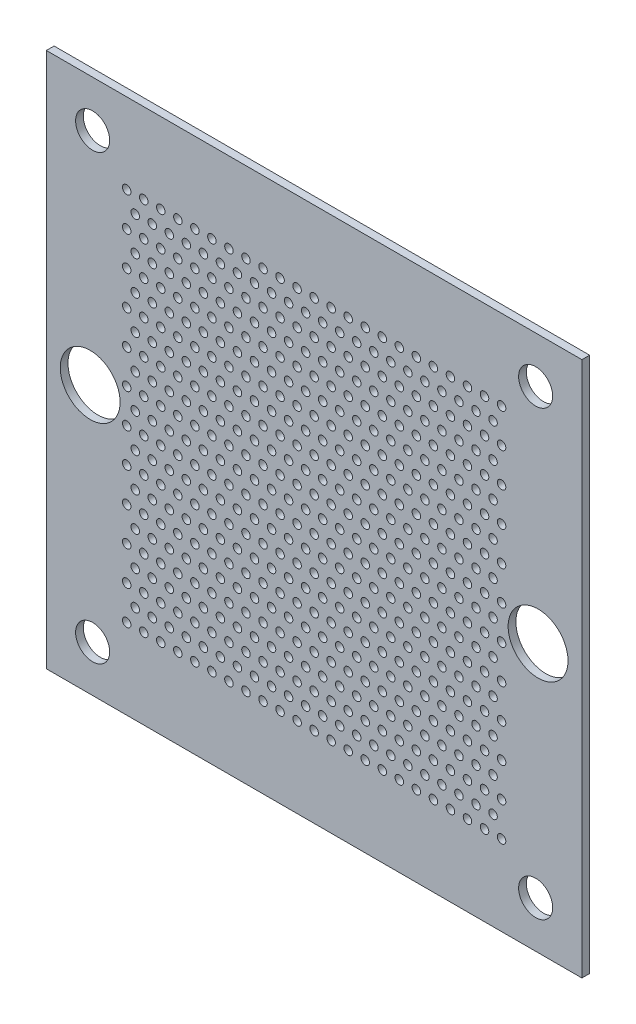
SolidWorks part; units mm, degrees
ref_plane "Front Plane" through (0, 0, 0) normal (0, 0, 1) x (1, 0, 0)
ref_plane "Top Plane" through (0, 0, 0) normal (0, 1, 0) x (1, 0, 0)
ref_plane "Right Plane" through (0, 0, 0) normal (1, 0, 0) x (0, 0, -1)
sketch "Model" plane through (0, 0, 0) normal (0, 0, 1) x (1, 0, 0)
  line L0 (-16.5, -16.5) -> (-16.5, 93.5)
  line L1 (-16.5, 93.5) -> (93.5, 93.5)
  line L2 (93.5, 93.5) -> (93.5, -16.5)
  line L3 (93.5, -16.5) -> (-16.5, -16.5)
  circle A0 centre (84, 84) radius 3.5
  circle A1 centre (-7, 84) radius 3.5
  circle A2 centre (-7, -7) radius 3.5
  circle A3 centre (84, -7) radius 3.5
  circle A4 centre (77, 0) radius 0.875
  circle A5 centre (73.5, 0) radius 0.875
  circle A6 centre (70, 0) radius 0.875
  circle A7 centre (66.5, 0) radius 0.875
  circle A8 centre (63, 0) radius 0.875
  circle A9 centre (59.5, 0) radius 0.875
  circle A10 centre (56, 0) radius 0.875
  circle A11 centre (52.5, 0) radius 0.875
  circle A12 centre (49, 0) radius 0.875
  circle A13 centre (45.5, 0) radius 0.875
  circle A14 centre (42, 0) radius 0.875
  circle A15 centre (38.5, 0) radius 0.875
  circle A16 centre (35, 0) radius 0.875
  circle A17 centre (31.5, 0) radius 0.875
  circle A18 centre (28, 0) radius 0.875
  circle A19 centre (24.5, 0) radius 0.875
  circle A20 centre (21, 0) radius 0.875
  circle A21 centre (17.5, 0) radius 0.875
  circle A22 centre (14, 0) radius 0.875
  circle A23 centre (10.5, 0) radius 0.875
  circle A24 centre (7, 0) radius 0.875
  circle A25 centre (3.5, 0) radius 0.875
  circle A26 centre (0, 0) radius 0.875
  circle A27 centre (75.25, 3.5) radius 0.875
  circle A28 centre (71.75, 3.5) radius 0.875
  circle A29 centre (68.25, 3.5) radius 0.875
  circle A30 centre (64.75, 3.5) radius 0.875
  circle A31 centre (61.25, 3.5) radius 0.875
  circle A32 centre (57.75, 3.5) radius 0.875
  circle A33 centre (54.25, 3.5) radius 0.875
  circle A34 centre (50.75, 3.5) radius 0.875
  circle A35 centre (47.25, 3.5) radius 0.875
  circle A36 centre (43.75, 3.5) radius 0.875
  circle A37 centre (40.25, 3.5) radius 0.875
  circle A38 centre (36.75, 3.5) radius 0.875
  circle A39 centre (33.25, 3.5) radius 0.875
  circle A40 centre (29.75, 3.5) radius 0.875
  circle A41 centre (26.25, 3.5) radius 0.875
  circle A42 centre (22.75, 3.5) radius 0.875
  circle A43 centre (19.25, 3.5) radius 0.875
  circle A44 centre (15.75, 3.5) radius 0.875
  circle A45 centre (12.25, 3.5) radius 0.875
  circle A46 centre (8.75, 3.5) radius 0.875
  circle A47 centre (5.25, 3.5) radius 0.875
  circle A48 centre (1.75, 3.5) radius 0.875
  circle A49 centre (77, 7) radius 0.875
  circle A50 centre (73.5, 7) radius 0.875
  circle A51 centre (70, 7) radius 0.875
  circle A52 centre (66.5, 7) radius 0.875
  circle A53 centre (63, 7) radius 0.875
  circle A54 centre (59.5, 7) radius 0.875
  circle A55 centre (56, 7) radius 0.875
  circle A56 centre (52.5, 7) radius 0.875
  circle A57 centre (49, 7) radius 0.875
  circle A58 centre (45.5, 7) radius 0.875
  circle A59 centre (42, 7) radius 0.875
  circle A60 centre (38.5, 7) radius 0.875
  circle A61 centre (35, 7) radius 0.875
  circle A62 centre (31.5, 7) radius 0.875
  circle A63 centre (28, 7) radius 0.875
  circle A64 centre (24.5, 7) radius 0.875
  circle A65 centre (21, 7) radius 0.875
  circle A66 centre (17.5, 7) radius 0.875
  circle A67 centre (14, 7) radius 0.875
  circle A68 centre (10.5, 7) radius 0.875
  circle A69 centre (7, 7) radius 0.875
  circle A70 centre (3.5, 7) radius 0.875
  circle A71 centre (0, 7) radius 0.875
  circle A72 centre (75.25, 10.5) radius 0.875
  circle A73 centre (71.75, 10.5) radius 0.875
  circle A74 centre (68.25, 10.5) radius 0.875
  circle A75 centre (64.75, 10.5) radius 0.875
  circle A76 centre (61.25, 10.5) radius 0.875
  circle A77 centre (57.75, 10.5) radius 0.875
  circle A78 centre (54.25, 10.5) radius 0.875
  circle A79 centre (50.75, 10.5) radius 0.875
  circle A80 centre (47.25, 10.5) radius 0.875
  circle A81 centre (43.75, 10.5) radius 0.875
  circle A82 centre (40.25, 10.5) radius 0.875
  circle A83 centre (36.75, 10.5) radius 0.875
  circle A84 centre (33.25, 10.5) radius 0.875
  circle A85 centre (29.75, 10.5) radius 0.875
  circle A86 centre (26.25, 10.5) radius 0.875
  circle A87 centre (22.75, 10.5) radius 0.875
  circle A88 centre (19.25, 10.5) radius 0.875
  circle A89 centre (15.75, 10.5) radius 0.875
  circle A90 centre (12.25, 10.5) radius 0.875
  circle A91 centre (8.75, 10.5) radius 0.875
  circle A92 centre (5.25, 10.5) radius 0.875
  circle A93 centre (1.75, 10.5) radius 0.875
  circle A94 centre (77, 14) radius 0.875
  circle A95 centre (73.5, 14) radius 0.875
  circle A96 centre (70, 14) radius 0.875
  circle A97 centre (66.5, 14) radius 0.875
  circle A98 centre (63, 14) radius 0.875
  circle A99 centre (59.5, 14) radius 0.875
  circle A100 centre (56, 14) radius 0.875
  circle A101 centre (52.5, 14) radius 0.875
  circle A102 centre (49, 14) radius 0.875
  circle A103 centre (45.5, 14) radius 0.875
  circle A104 centre (42, 14) radius 0.875
  circle A105 centre (38.5, 14) radius 0.875
  circle A106 centre (35, 14) radius 0.875
  circle A107 centre (31.5, 14) radius 0.875
  circle A108 centre (28, 14) radius 0.875
  circle A109 centre (24.5, 14) radius 0.875
  circle A110 centre (21, 14) radius 0.875
  circle A111 centre (17.5, 14) radius 0.875
  circle A112 centre (14, 14) radius 0.875
  circle A113 centre (10.5, 14) radius 0.875
  circle A114 centre (7, 14) radius 0.875
  circle A115 centre (3.5, 14) radius 0.875
  circle A116 centre (0, 14) radius 0.875
  circle A117 centre (75.25, 17.5) radius 0.875
  circle A118 centre (71.75, 17.5) radius 0.875
  circle A119 centre (68.25, 17.5) radius 0.875
  circle A120 centre (64.75, 17.5) radius 0.875
  circle A121 centre (61.25, 17.5) radius 0.875
  circle A122 centre (57.75, 17.5) radius 0.875
  circle A123 centre (54.25, 17.5) radius 0.875
  circle A124 centre (50.75, 17.5) radius 0.875
  circle A125 centre (47.25, 17.5) radius 0.875
  circle A126 centre (43.75, 17.5) radius 0.875
  circle A127 centre (40.25, 17.5) radius 0.875
  circle A128 centre (36.75, 17.5) radius 0.875
  circle A129 centre (33.25, 17.5) radius 0.875
  circle A130 centre (29.75, 17.5) radius 0.875
  circle A131 centre (26.25, 17.5) radius 0.875
  circle A132 centre (22.75, 17.5) radius 0.875
  circle A133 centre (19.25, 17.5) radius 0.875
  circle A134 centre (15.75, 17.5) radius 0.875
  circle A135 centre (12.25, 17.5) radius 0.875
  circle A136 centre (8.75, 17.5) radius 0.875
  circle A137 centre (5.25, 17.5) radius 0.875
  circle A138 centre (1.75, 17.5) radius 0.875
  circle A139 centre (77, 21) radius 0.875
  circle A140 centre (73.5, 21) radius 0.875
  circle A141 centre (70, 21) radius 0.875
  circle A142 centre (66.5, 21) radius 0.875
  circle A143 centre (63, 21) radius 0.875
  circle A144 centre (59.5, 21) radius 0.875
  circle A145 centre (56, 21) radius 0.875
  circle A146 centre (52.5, 21) radius 0.875
  circle A147 centre (49, 21) radius 0.875
  circle A148 centre (45.5, 21) radius 0.875
  circle A149 centre (42, 21) radius 0.875
  circle A150 centre (38.5, 21) radius 0.875
  circle A151 centre (35, 21) radius 0.875
  circle A152 centre (31.5, 21) radius 0.875
  circle A153 centre (28, 21) radius 0.875
  circle A154 centre (24.5, 21) radius 0.875
  circle A155 centre (21, 21) radius 0.875
  circle A156 centre (17.5, 21) radius 0.875
  circle A157 centre (14, 21) radius 0.875
  circle A158 centre (10.5, 21) radius 0.875
  circle A159 centre (7, 21) radius 0.875
  circle A160 centre (3.5, 21) radius 0.875
  circle A161 centre (0, 21) radius 0.875
  circle A162 centre (75.25, 24.5) radius 0.875
  circle A163 centre (71.75, 24.5) radius 0.875
  circle A164 centre (68.25, 24.5) radius 0.875
  circle A165 centre (64.75, 24.5) radius 0.875
  circle A166 centre (61.25, 24.5) radius 0.875
  circle A167 centre (57.75, 24.5) radius 0.875
  circle A168 centre (54.25, 24.5) radius 0.875
  circle A169 centre (50.75, 24.5) radius 0.875
  circle A170 centre (47.25, 24.5) radius 0.875
  circle A171 centre (43.75, 24.5) radius 0.875
  circle A172 centre (40.25, 24.5) radius 0.875
  circle A173 centre (36.75, 24.5) radius 0.875
  circle A174 centre (33.25, 24.5) radius 0.875
  circle A175 centre (29.75, 24.5) radius 0.875
  circle A176 centre (26.25, 24.5) radius 0.875
  circle A177 centre (22.75, 24.5) radius 0.875
  circle A178 centre (19.25, 24.5) radius 0.875
  circle A179 centre (15.75, 24.5) radius 0.875
  circle A180 centre (12.25, 24.5) radius 0.875
  circle A181 centre (8.75, 24.5) radius 0.875
  circle A182 centre (5.25, 24.5) radius 0.875
  circle A183 centre (1.75, 24.5) radius 0.875
  circle A184 centre (77, 28) radius 0.875
  circle A185 centre (73.5, 28) radius 0.875
  circle A186 centre (70, 28) radius 0.875
  circle A187 centre (66.5, 28) radius 0.875
  circle A188 centre (63, 28) radius 0.875
  circle A189 centre (59.5, 28) radius 0.875
  circle A190 centre (56, 28) radius 0.875
  circle A191 centre (52.5, 28) radius 0.875
  circle A192 centre (49, 28) radius 0.875
  circle A193 centre (45.5, 28) radius 0.875
  circle A194 centre (42, 28) radius 0.875
  circle A195 centre (38.5, 28) radius 0.875
  circle A196 centre (35, 28) radius 0.875
  circle A197 centre (31.5, 28) radius 0.875
  circle A198 centre (28, 28) radius 0.875
  circle A199 centre (24.5, 28) radius 0.875
  circle A200 centre (21, 28) radius 0.875
  circle A201 centre (17.5, 28) radius 0.875
  circle A202 centre (14, 28) radius 0.875
  circle A203 centre (10.5, 28) radius 0.875
  circle A204 centre (7, 28) radius 0.875
  circle A205 centre (3.5, 28) radius 0.875
  circle A206 centre (0, 28) radius 0.875
  circle A207 centre (75.25, 31.5) radius 0.875
  circle A208 centre (71.75, 31.5) radius 0.875
  circle A209 centre (68.25, 31.5) radius 0.875
  circle A210 centre (64.75, 31.5) radius 0.875
  circle A211 centre (61.25, 31.5) radius 0.875
  circle A212 centre (57.75, 31.5) radius 0.875
  circle A213 centre (54.25, 31.5) radius 0.875
  circle A214 centre (50.75, 31.5) radius 0.875
  circle A215 centre (47.25, 31.5) radius 0.875
  circle A216 centre (43.75, 31.5) radius 0.875
  circle A217 centre (40.25, 31.5) radius 0.875
  circle A218 centre (36.75, 31.5) radius 0.875
  circle A219 centre (33.25, 31.5) radius 0.875
  circle A220 centre (29.75, 31.5) radius 0.875
  circle A221 centre (26.25, 31.5) radius 0.875
  circle A222 centre (22.75, 31.5) radius 0.875
  circle A223 centre (19.25, 31.5) radius 0.875
  circle A224 centre (15.75, 31.5) radius 0.875
  circle A225 centre (12.25, 31.5) radius 0.875
  circle A226 centre (8.75, 31.5) radius 0.875
  circle A227 centre (5.25, 31.5) radius 0.875
  circle A228 centre (1.75, 31.5) radius 0.875
  circle A229 centre (77, 35) radius 0.875
  circle A230 centre (73.5, 35) radius 0.875
  circle A231 centre (70, 35) radius 0.875
  circle A232 centre (66.5, 35) radius 0.875
  circle A233 centre (63, 35) radius 0.875
  circle A234 centre (59.5, 35) radius 0.875
  circle A235 centre (56, 35) radius 0.875
  circle A236 centre (52.5, 35) radius 0.875
  circle A237 centre (49, 35) radius 0.875
  circle A238 centre (45.5, 35) radius 0.875
  circle A239 centre (42, 35) radius 0.875
  circle A240 centre (38.5, 35) radius 0.875
  circle A241 centre (35, 35) radius 0.875
  circle A242 centre (31.5, 35) radius 0.875
  circle A243 centre (28, 35) radius 0.875
  circle A244 centre (24.5, 35) radius 0.875
  circle A245 centre (21, 35) radius 0.875
  circle A246 centre (17.5, 35) radius 0.875
  circle A247 centre (14, 35) radius 0.875
  circle A248 centre (10.5, 35) radius 0.875
  circle A249 centre (7, 35) radius 0.875
  circle A250 centre (3.5, 35) radius 0.875
  circle A251 centre (0, 35) radius 0.875
  circle A252 centre (75.25, 38.5) radius 0.875
  circle A253 centre (71.75, 38.5) radius 0.875
  circle A254 centre (68.25, 38.5) radius 0.875
  circle A255 centre (64.75, 38.5) radius 0.875
  circle A256 centre (61.25, 38.5) radius 0.875
  circle A257 centre (57.75, 38.5) radius 0.875
  circle A258 centre (54.25, 38.5) radius 0.875
  circle A259 centre (50.75, 38.5) radius 0.875
  circle A260 centre (47.25, 38.5) radius 0.875
  circle A261 centre (43.75, 38.5) radius 0.875
  circle A262 centre (40.25, 38.5) radius 0.875
  circle A263 centre (36.75, 38.5) radius 0.875
  circle A264 centre (33.25, 38.5) radius 0.875
  circle A265 centre (29.75, 38.5) radius 0.875
  circle A266 centre (26.25, 38.5) radius 0.875
  circle A267 centre (22.75, 38.5) radius 0.875
  circle A268 centre (19.25, 38.5) radius 0.875
  circle A269 centre (15.75, 38.5) radius 0.875
  circle A270 centre (12.25, 38.5) radius 0.875
  circle A271 centre (8.75, 38.5) radius 0.875
  circle A272 centre (5.25, 38.5) radius 0.875
  circle A273 centre (1.75, 38.5) radius 0.875
  circle A274 centre (77, 42) radius 0.875
  circle A275 centre (73.5, 42) radius 0.875
  circle A276 centre (70, 42) radius 0.875
  circle A277 centre (66.5, 42) radius 0.875
  circle A278 centre (63, 42) radius 0.875
  circle A279 centre (59.5, 42) radius 0.875
  circle A280 centre (56, 42) radius 0.875
  circle A281 centre (52.5, 42) radius 0.875
  circle A282 centre (49, 42) radius 0.875
  circle A283 centre (45.5, 42) radius 0.875
  circle A284 centre (42, 42) radius 0.875
  circle A285 centre (38.5, 42) radius 0.875
  circle A286 centre (35, 42) radius 0.875
  circle A287 centre (31.5, 42) radius 0.875
  circle A288 centre (28, 42) radius 0.875
  circle A289 centre (24.5, 42) radius 0.875
  circle A290 centre (21, 42) radius 0.875
  circle A291 centre (17.5, 42) radius 0.875
  circle A292 centre (14, 42) radius 0.875
  circle A293 centre (10.5, 42) radius 0.875
  circle A294 centre (7, 42) radius 0.875
  circle A295 centre (3.5, 42) radius 0.875
  circle A296 centre (0, 42) radius 0.875
  circle A297 centre (75.25, 45.5) radius 0.875
  circle A298 centre (71.75, 45.5) radius 0.875
  circle A299 centre (68.25, 45.5) radius 0.875
  circle A300 centre (64.75, 45.5) radius 0.875
  circle A301 centre (61.25, 45.5) radius 0.875
  circle A302 centre (57.75, 45.5) radius 0.875
  circle A303 centre (54.25, 45.5) radius 0.875
  circle A304 centre (50.75, 45.5) radius 0.875
  circle A305 centre (47.25, 45.5) radius 0.875
  circle A306 centre (43.75, 45.5) radius 0.875
  circle A307 centre (40.25, 45.5) radius 0.875
  circle A308 centre (36.75, 45.5) radius 0.875
  circle A309 centre (33.25, 45.5) radius 0.875
  circle A310 centre (29.75, 45.5) radius 0.875
  circle A311 centre (26.25, 45.5) radius 0.875
  circle A312 centre (22.75, 45.5) radius 0.875
  circle A313 centre (19.25, 45.5) radius 0.875
  circle A314 centre (15.75, 45.5) radius 0.875
  circle A315 centre (12.25, 45.5) radius 0.875
  circle A316 centre (8.75, 45.5) radius 0.875
  circle A317 centre (5.25, 45.5) radius 0.875
  circle A318 centre (1.75, 45.5) radius 0.875
  circle A319 centre (77, 49) radius 0.875
  circle A320 centre (73.5, 49) radius 0.875
  circle A321 centre (70, 49) radius 0.875
  circle A322 centre (66.5, 49) radius 0.875
  circle A323 centre (63, 49) radius 0.875
  circle A324 centre (59.5, 49) radius 0.875
  circle A325 centre (56, 49) radius 0.875
  circle A326 centre (52.5, 49) radius 0.875
  circle A327 centre (49, 49) radius 0.875
  circle A328 centre (45.5, 49) radius 0.875
  circle A329 centre (42, 49) radius 0.875
  circle A330 centre (38.5, 49) radius 0.875
  circle A331 centre (35, 49) radius 0.875
  circle A332 centre (31.5, 49) radius 0.875
  circle A333 centre (28, 49) radius 0.875
  circle A334 centre (24.5, 49) radius 0.875
  circle A335 centre (21, 49) radius 0.875
  circle A336 centre (17.5, 49) radius 0.875
  circle A337 centre (14, 49) radius 0.875
  circle A338 centre (10.5, 49) radius 0.875
  circle A339 centre (7, 49) radius 0.875
  circle A340 centre (3.5, 49) radius 0.875
  circle A341 centre (0, 49) radius 0.875
  circle A342 centre (75.25, 52.5) radius 0.875
  circle A343 centre (71.75, 52.5) radius 0.875
  circle A344 centre (68.25, 52.5) radius 0.875
  circle A345 centre (64.75, 52.5) radius 0.875
  circle A346 centre (61.25, 52.5) radius 0.875
  circle A347 centre (57.75, 52.5) radius 0.875
  circle A348 centre (54.25, 52.5) radius 0.875
  circle A349 centre (50.75, 52.5) radius 0.875
  circle A350 centre (47.25, 52.5) radius 0.875
  circle A351 centre (43.75, 52.5) radius 0.875
  circle A352 centre (40.25, 52.5) radius 0.875
  circle A353 centre (36.75, 52.5) radius 0.875
  circle A354 centre (33.25, 52.5) radius 0.875
  circle A355 centre (29.75, 52.5) radius 0.875
  circle A356 centre (26.25, 52.5) radius 0.875
  circle A357 centre (22.75, 52.5) radius 0.875
  circle A358 centre (19.25, 52.5) radius 0.875
  circle A359 centre (15.75, 52.5) radius 0.875
  circle A360 centre (12.25, 52.5) radius 0.875
  circle A361 centre (8.75, 52.5) radius 0.875
  circle A362 centre (5.25, 52.5) radius 0.875
  circle A363 centre (1.75, 52.5) radius 0.875
  circle A364 centre (77, 56) radius 0.875
  circle A365 centre (73.5, 56) radius 0.875
  circle A366 centre (70, 56) radius 0.875
  circle A367 centre (66.5, 56) radius 0.875
  circle A368 centre (63, 56) radius 0.875
  circle A369 centre (59.5, 56) radius 0.875
  circle A370 centre (56, 56) radius 0.875
  circle A371 centre (52.5, 56) radius 0.875
  circle A372 centre (49, 56) radius 0.875
  circle A373 centre (45.5, 56) radius 0.875
  circle A374 centre (42, 56) radius 0.875
  circle A375 centre (38.5, 56) radius 0.875
  circle A376 centre (35, 56) radius 0.875
  circle A377 centre (31.5, 56) radius 0.875
  circle A378 centre (28, 56) radius 0.875
  circle A379 centre (24.5, 56) radius 0.875
  circle A380 centre (21, 56) radius 0.875
  circle A381 centre (17.5, 56) radius 0.875
  circle A382 centre (14, 56) radius 0.875
  circle A383 centre (10.5, 56) radius 0.875
  circle A384 centre (7, 56) radius 0.875
  circle A385 centre (3.5, 56) radius 0.875
  circle A386 centre (0, 56) radius 0.875
  circle A387 centre (75.25, 59.5) radius 0.875
  circle A388 centre (71.75, 59.5) radius 0.875
  circle A389 centre (68.25, 59.5) radius 0.875
  circle A390 centre (64.75, 59.5) radius 0.875
  circle A391 centre (61.25, 59.5) radius 0.875
  circle A392 centre (57.75, 59.5) radius 0.875
  circle A393 centre (54.25, 59.5) radius 0.875
  circle A394 centre (50.75, 59.5) radius 0.875
  circle A395 centre (47.25, 59.5) radius 0.875
  circle A396 centre (43.75, 59.5) radius 0.875
  circle A397 centre (40.25, 59.5) radius 0.875
  circle A398 centre (36.75, 59.5) radius 0.875
  circle A399 centre (33.25, 59.5) radius 0.875
  circle A400 centre (29.75, 59.5) radius 0.875
  circle A401 centre (26.25, 59.5) radius 0.875
  circle A402 centre (22.75, 59.5) radius 0.875
  circle A403 centre (19.25, 59.5) radius 0.875
  circle A404 centre (15.75, 59.5) radius 0.875
  circle A405 centre (12.25, 59.5) radius 0.875
  circle A406 centre (8.75, 59.5) radius 0.875
  circle A407 centre (5.25, 59.5) radius 0.875
  circle A408 centre (1.75, 59.5) radius 0.875
  circle A409 centre (77, 63) radius 0.875
  circle A410 centre (73.5, 63) radius 0.875
  circle A411 centre (70, 63) radius 0.875
  circle A412 centre (66.5, 63) radius 0.875
  circle A413 centre (63, 63) radius 0.875
  circle A414 centre (59.5, 63) radius 0.875
  circle A415 centre (56, 63) radius 0.875
  circle A416 centre (52.5, 63) radius 0.875
  circle A417 centre (49, 63) radius 0.875
  circle A418 centre (45.5, 63) radius 0.875
  circle A419 centre (42, 63) radius 0.875
  circle A420 centre (38.5, 63) radius 0.875
  circle A421 centre (35, 63) radius 0.875
  circle A422 centre (31.5, 63) radius 0.875
  circle A423 centre (28, 63) radius 0.875
  circle A424 centre (24.5, 63) radius 0.875
  circle A425 centre (21, 63) radius 0.875
  circle A426 centre (17.5, 63) radius 0.875
  circle A427 centre (14, 63) radius 0.875
  circle A428 centre (10.5, 63) radius 0.875
  circle A429 centre (7, 63) radius 0.875
  circle A430 centre (3.5, 63) radius 0.875
  circle A431 centre (0, 63) radius 0.875
  circle A432 centre (75.25, 66.5) radius 0.875
  circle A433 centre (71.75, 66.5) radius 0.875
  circle A434 centre (68.25, 66.5) radius 0.875
  circle A435 centre (64.75, 66.5) radius 0.875
  circle A436 centre (61.25, 66.5) radius 0.875
  circle A437 centre (57.75, 66.5) radius 0.875
  circle A438 centre (54.25, 66.5) radius 0.875
  circle A439 centre (50.75, 66.5) radius 0.875
  circle A440 centre (47.25, 66.5) radius 0.875
  circle A441 centre (43.75, 66.5) radius 0.875
  circle A442 centre (40.25, 66.5) radius 0.875
  circle A443 centre (36.75, 66.5) radius 0.875
  circle A444 centre (33.25, 66.5) radius 0.875
  circle A445 centre (29.75, 66.5) radius 0.875
  circle A446 centre (26.25, 66.5) radius 0.875
  circle A447 centre (22.75, 66.5) radius 0.875
  circle A448 centre (19.25, 66.5) radius 0.875
  circle A449 centre (15.75, 66.5) radius 0.875
  circle A450 centre (12.25, 66.5) radius 0.875
  circle A451 centre (8.75, 66.5) radius 0.875
  circle A452 centre (5.25, 66.5) radius 0.875
  circle A453 centre (1.75, 66.5) radius 0.875
  circle A454 centre (77, 70) radius 0.875
  circle A455 centre (73.5, 70) radius 0.875
  circle A456 centre (70, 70) radius 0.875
  circle A457 centre (66.5, 70) radius 0.875
  circle A458 centre (63, 70) radius 0.875
  circle A459 centre (59.5, 70) radius 0.875
  circle A460 centre (56, 70) radius 0.875
  circle A461 centre (52.5, 70) radius 0.875
  circle A462 centre (49, 70) radius 0.875
  circle A463 centre (45.5, 70) radius 0.875
  circle A464 centre (42, 70) radius 0.875
  circle A465 centre (38.5, 70) radius 0.875
  circle A466 centre (35, 70) radius 0.875
  circle A467 centre (31.5, 70) radius 0.875
  circle A468 centre (28, 70) radius 0.875
  circle A469 centre (24.5, 70) radius 0.875
  circle A470 centre (21, 70) radius 0.875
  circle A471 centre (17.5, 70) radius 0.875
  circle A472 centre (14, 70) radius 0.875
  circle A473 centre (10.5, 70) radius 0.875
  circle A474 centre (7, 70) radius 0.875
  circle A475 centre (3.5, 70) radius 0.875
  circle A476 centre (0, 70) radius 0.875
  circle A477 centre (75.25, 73.5) radius 0.875
  circle A478 centre (71.75, 73.5) radius 0.875
  circle A479 centre (68.25, 73.5) radius 0.875
  circle A480 centre (64.75, 73.5) radius 0.875
  circle A481 centre (61.25, 73.5) radius 0.875
  circle A482 centre (57.75, 73.5) radius 0.875
  circle A483 centre (54.25, 73.5) radius 0.875
  circle A484 centre (50.75, 73.5) radius 0.875
  circle A485 centre (47.25, 73.5) radius 0.875
  circle A486 centre (43.75, 73.5) radius 0.875
  circle A487 centre (40.25, 73.5) radius 0.875
  circle A488 centre (36.75, 73.5) radius 0.875
  circle A489 centre (33.25, 73.5) radius 0.875
  circle A490 centre (29.75, 73.5) radius 0.875
  circle A491 centre (26.25, 73.5) radius 0.875
  circle A492 centre (22.75, 73.5) radius 0.875
  circle A493 centre (19.25, 73.5) radius 0.875
  circle A494 centre (15.75, 73.5) radius 0.875
  circle A495 centre (12.25, 73.5) radius 0.875
  circle A496 centre (8.75, 73.5) radius 0.875
  circle A497 centre (5.25, 73.5) radius 0.875
  circle A498 centre (1.75, 73.5) radius 0.875
  circle A499 centre (77, 77) radius 0.875
  circle A500 centre (73.5, 77) radius 0.875
  circle A501 centre (70, 77) radius 0.875
  circle A502 centre (66.5, 77) radius 0.875
  circle A503 centre (63, 77) radius 0.875
  circle A504 centre (59.5, 77) radius 0.875
  circle A505 centre (56, 77) radius 0.875
  circle A506 centre (52.5, 77) radius 0.875
  circle A507 centre (49, 77) radius 0.875
  circle A508 centre (45.5, 77) radius 0.875
  circle A509 centre (42, 77) radius 0.875
  circle A510 centre (38.5, 77) radius 0.875
  circle A511 centre (35, 77) radius 0.875
  circle A512 centre (31.5, 77) radius 0.875
  circle A513 centre (28, 77) radius 0.875
  circle A514 centre (24.5, 77) radius 0.875
  circle A515 centre (21, 77) radius 0.875
  circle A516 centre (17.5, 77) radius 0.875
  circle A517 centre (14, 77) radius 0.875
  circle A518 centre (10.5, 77) radius 0.875
  circle A519 centre (7, 77) radius 0.875
  circle A520 centre (3.5, 77) radius 0.875
  circle A521 centre (0, 77) radius 0.875
  circle A526 centre (-7.5, 38.5) radius 6.15
  circle A527 centre (84.5, 38.5) radius 6.15
extrude "Boss-Extrude1" add sketch "Model" along normal blind 1.5875
